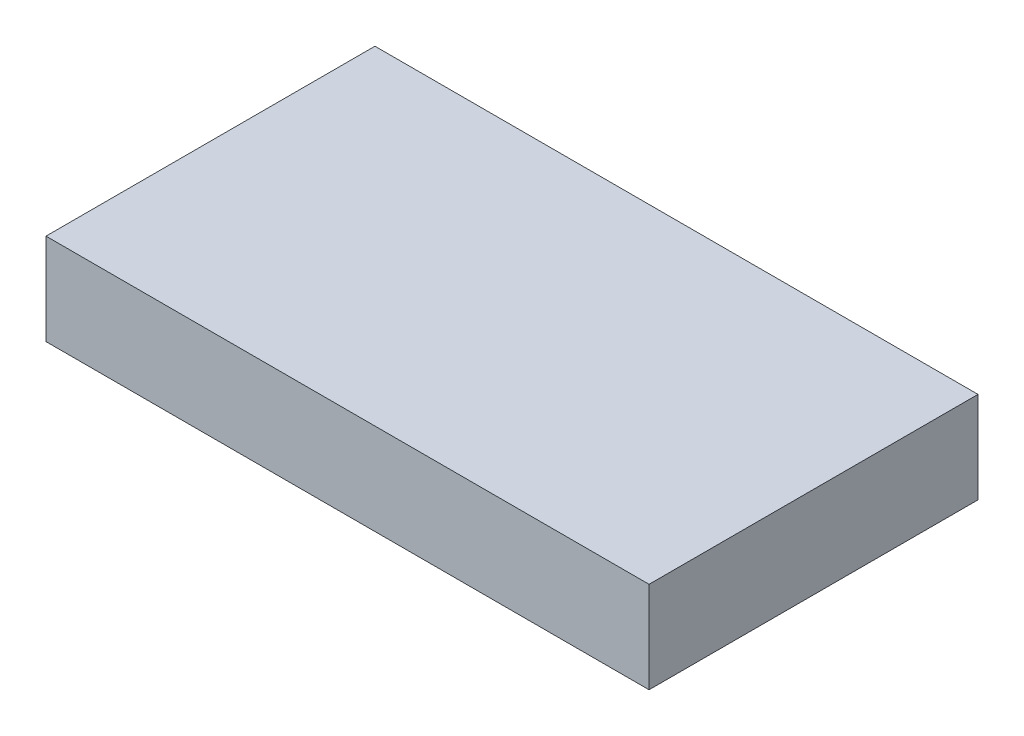
SolidWorks part; units mm, degrees
ref_plane "Front Plane" through (0, 0, 0) normal (0, 0, 1) x (1, 0, 0)
ref_plane "Top Plane" through (0, 0, 0) normal (0, 1, 0) x (1, 0, 0)
ref_plane "Right Plane" through (0, 0, 0) normal (1, 0, 0) x (0, 0, -1)
sketch "Sketch1" plane through (0, 0, 0) normal (0, 1, 0) x (1, 0, 0)
  line L1 (0, 0) -> (66, 0)
  line L2 (0, 0) -> (0, 36)
  line L3 (0, 36) -> (66, 36)
  line L4 (66, 0) -> (66, 36)
  dimension "D1" = 36
  dimension "D2" = 66
extrude "Boss-Extrude1" add sketch "Sketch1" along normal blind 10
